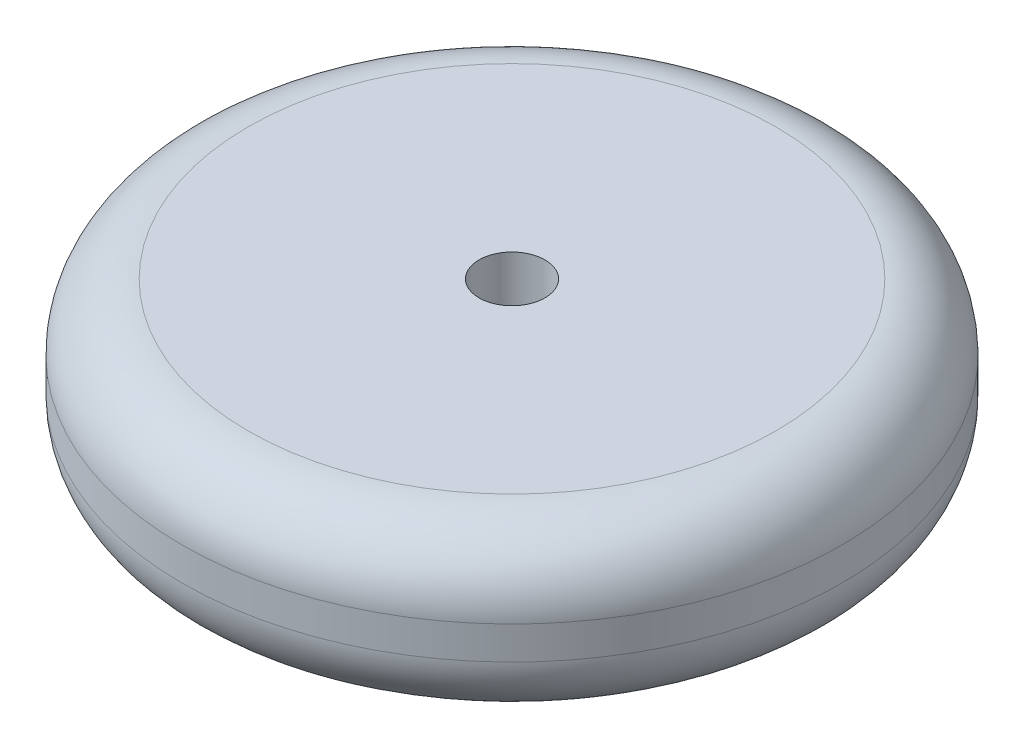
SolidWorks part; units mm, degrees
ref_plane "前视基准面" through (0, 0, 0) normal (0, 0, 1) x (1, 0, 0)
ref_plane "上视基准面" through (0, 0, 0) normal (0, 1, 0) x (1, 0, 0)
ref_plane "右视基准面" through (0, 0, 0) normal (1, 0, 0) x (0, 0, -1)
sketch "草图1" plane through (0, 0, 0) normal (0, 1, 0) x (1, 0, 0)
  circle A0 centre (0, 0) radius 40
  dimension "D1" = 80
extrude "凸台-拉伸1" add sketch "草图1" along normal mid plane 20 contours A0
fillet "圆角1" radius 8 2 edges at (0, 10, 40) (0, -10, 40)
sketch "草图2" plane through (0, 0, 0) normal (0, 1, 0) x (1, 0, 0)
  circle A0 centre (0, 0) radius 4
  dimension "D1" = 8
extrude "切除-拉伸1" cut sketch "草图2" against normal mid plane 20
